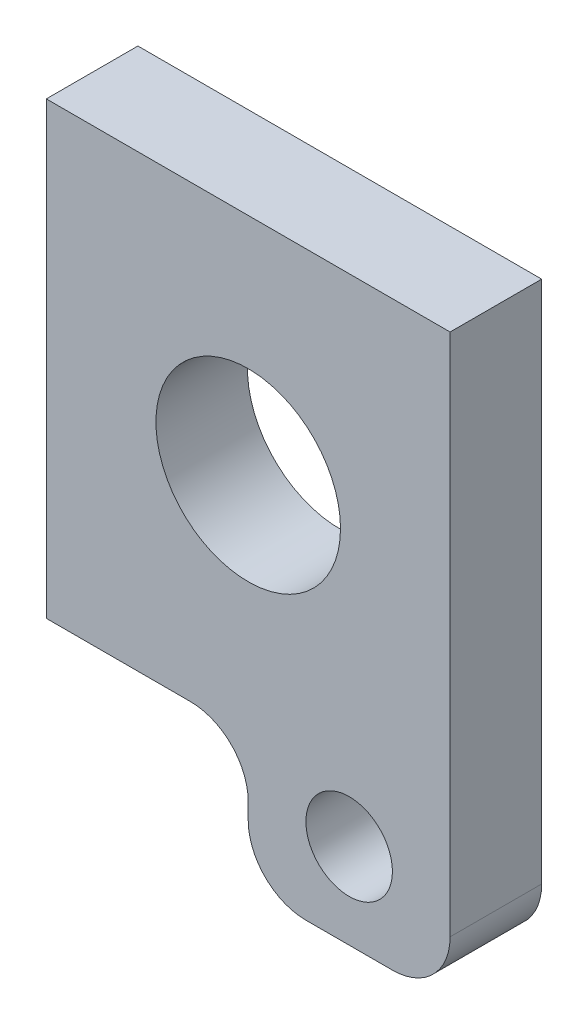
SolidWorks part; units mm, degrees
ref_plane "Front Plane" through (0, 0, 0) normal (0, 0, 1) x (1, 0, 0)
ref_plane "Top Plane" through (0, 0, 0) normal (0, 1, 0) x (1, 0, 0)
ref_plane "Right Plane" through (0, 0, 0) normal (1, 0, 0) x (0, 0, -1)
ref_plane "Plane1" through (0, 0, 0) normal (0, 0, -1) x (-1, 0, 0)
sketch "Sketch1" plane through (0, 0, 0) normal (0, 0, -1) x (-1, 0, 0)
  line L0 (3.5, -3.9) -> (3.5, 3.9)
  line L1 (3.5, 3.9) -> (-3.5, 3.9)
  line L2 (-3.5, 3.9) -> (-3.5, -5.1813)
  line L3 (-2.5, -6.1812) -> (-1, -6.1812)
  line L4 (0, -5.1812) -> (0, -4.9)
  line L5 (1, -3.9) -> (3.5, -3.9)
  circle A0 centre (-1.75, -4.7) radius 0.75
  arc A1 (-3.5, -5.1813) -> (-2.5, -6.1812) centre (-2.5, -5.1812) ccw
  arc A2 (-1, -6.1812) -> (0, -5.1812) centre (-1, -5.1812) ccw
  arc A3 (0, -4.9) -> (1, -3.9) centre (1, -4.9) cw
  circle A4 centre (0, 0) radius 1.6
extrude "Boss-Extrude1" add sketch "Sketch1" against normal blind 1.5875
